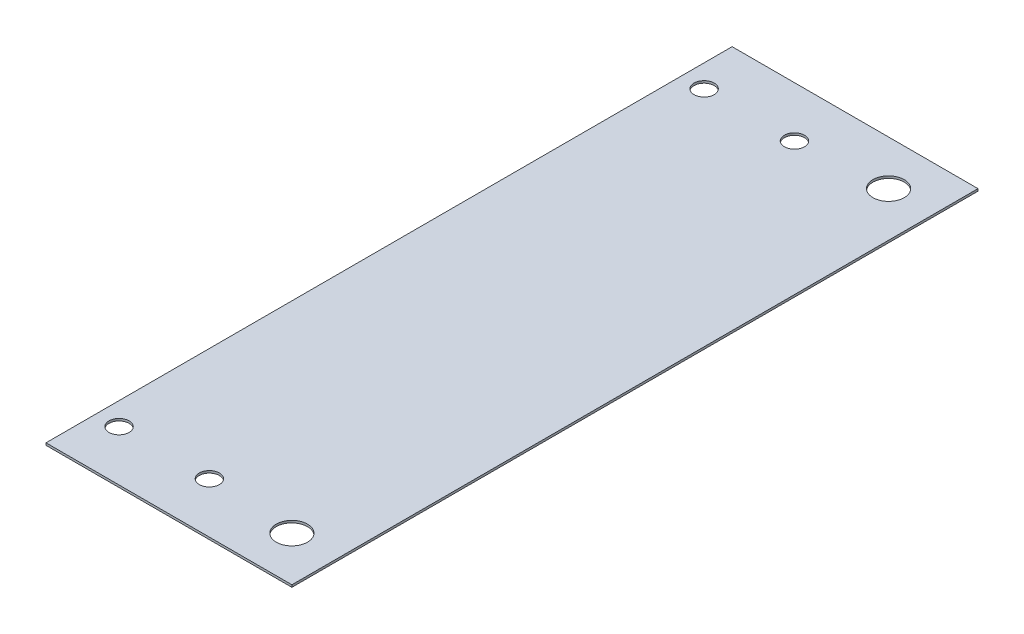
SolidWorks part; units mm, degrees
ref_plane "Front Plane" through (0, 0, 0) normal (0, 0, 1) x (1, 0, 0)
ref_plane "Top Plane" through (0, 0, 0) normal (0, 1, 0) x (1, 0, 0)
ref_plane "Right Plane" through (0, 0, 0) normal (1, 0, 0) x (0, 0, -1)
sketch "Sketch1" plane through (0, 0, 0) normal (0, 1, 0) x (1, 0, 0)
  line L1 (-13.75, 38.3675) -> (13.75, 38.3675)
  line L2 (-13.75, 38.3675) -> (-13.75, -38.3675)
  line L3 (-13.75, -38.3675) -> (13.75, -38.3675)
  line L4 (13.75, 38.3675) -> (13.75, -38.3675)
  line L5 (-13.75, 38.3675) -> (13.75, -38.3675) construction
  line L6 (-13.75, -38.3675) -> (13.75, 38.3675) construction
  circle A1 centre (-11.23, 32.7175) radius 1.125
  circle A2 centre (-1.13, 32.7175) radius 1.125
  circle A3 centre (8.75, 33.3675) radius 1.75
  circle A7 centre (8.75, -33.3675) radius 1.75
  circle A8 centre (-11.23, -32.7175) radius 1.125
  circle A9 centre (-1.13, -32.7175) radius 1.125
  point P0 (0, 0)
  dimension "D3" = 3.5
  dimension "D4" = 2.25
  dimension "D1" = 76.735
  dimension "D2" = 27.5
  dimension "D5" = 5.65
  dimension "D6" = 5.65
  dimension "D7" = 5
  dimension "D8" = 5
  dimension "D9" = 5
  dimension "D10" = 9.88
  dimension "D11" = 10.1
extrude "Boss-Extrude1" add sketch "Sketch1" along normal blind 0.25
